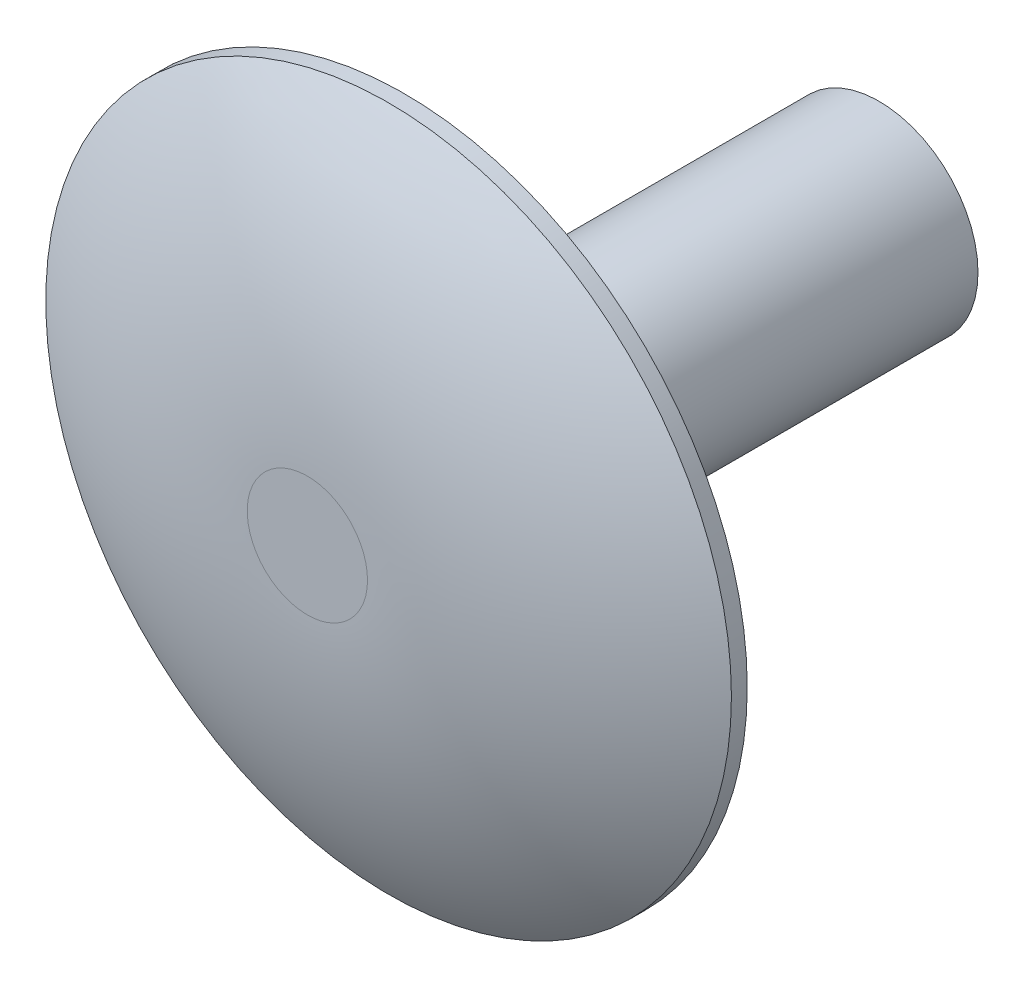
SolidWorks part; units mm, degrees
material "6061 Alloy"
ref_plane "Front Plane" through (0, 0, 0) normal (0, 0, 1) x (1, 0, 0)
ref_plane "Top Plane" through (0, 0, 0) normal (0, 1, 0) x (1, 0, 0)
ref_plane "Right Plane" through (0, 0, 0) normal (1, 0, 0) x (0, 0, -1)
sketch "Sketch1" plane through (0, 0, 0) normal (0, 0, 1) x (1, 0, 0)
  circle A0 centre (0, 0) radius 8.255
  dimension "D1" = 16.51
extrude "Boss-Extrude1" add sketch "Sketch1" along normal blind 2.3368
sketch "Sketch2" plane through (0, 0, 0) normal (0, 0, 1) x (1, 0, 0)
  circle A0 centre (0, 0) radius 2.3813
  dimension "D1" = 4.7625
extrude "Boss-Extrude2" add sketch "Sketch2" against normal blind 11.43
sketch "Sketch3" plane through (0, 0, 0) normal (0, 1, 0) x (1, 0, 0)
  line L0 (0, -2.3368) -> (1.4478, -2.3368)
  line L1 (-8.255, -2.3368) -> (8.255, -2.3368) construction
  line L2 (0, -2.3368) -> (0, 0) construction
  line L3 (8.255, -2.3368) -> (8.255, 0) construction
  line L4 (8.255, -0.381) -> (8.255, 0)
  line L5 (8.255, 0) -> (-8.255, 0) construction
  line L6 (8.255, -0.381) -> (8.255, -2.3368)
  line L7 (8.255, -2.3368) -> (1.4478, -2.3368)
  arc A0 (1.4478, -2.3368) -> (8.255, -0.381) centre (1.4478, 10.4874) ccw
  dimension "D1" = 2.8956
  dimension "D2" = 0.381
revolve "Cut-Revolve1" cut sketch "Sketch3" angle 360 about L2
